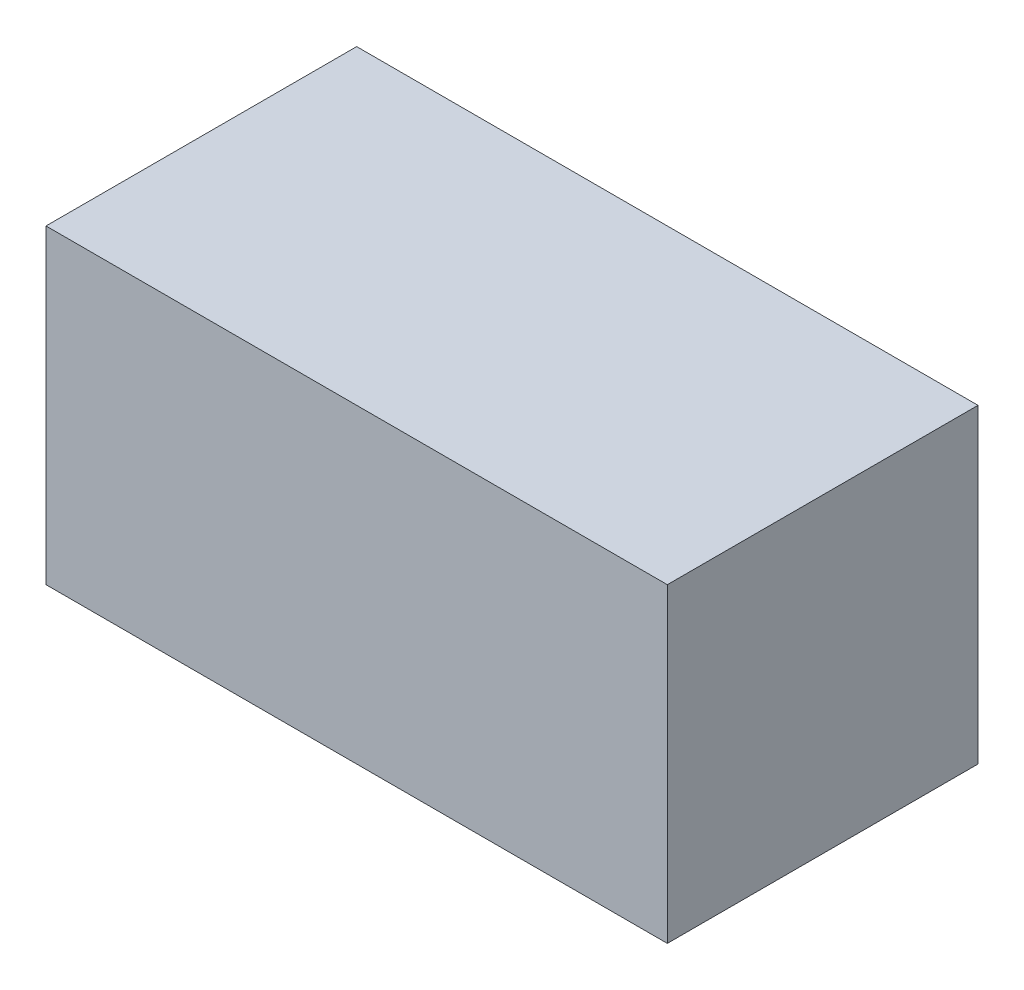
SolidWorks part; units mm, degrees
ref_plane "Front Plane" through (0, 0, 0) normal (0, 0, 1) x (1, 0, 0)
ref_plane "Top Plane" through (0, 0, 0) normal (0, 1, 0) x (1, 0, 0)
ref_plane "Right Plane" through (0, 0, 0) normal (1, 0, 0) x (0, 0, -1)
sketch "Sketch1" plane through (0, 0, 0) normal (0, 1, 0) x (1, 0, 0)
  line L1 (-20, 10) -> (20, 10)
  line L2 (-20, 10) -> (-20, -10)
  line L3 (-20, -10) -> (20, -10)
  line L4 (20, 10) -> (20, -10)
  line L5 (-20, 10) -> (20, -10) construction
  line L6 (-20, -10) -> (20, 10) construction
  point P4 (0, 0)
  dimension "D1" = 40
  dimension "D2" = 20
extrude "Heater Body" add sketch "Sketch1" along normal blind 20
